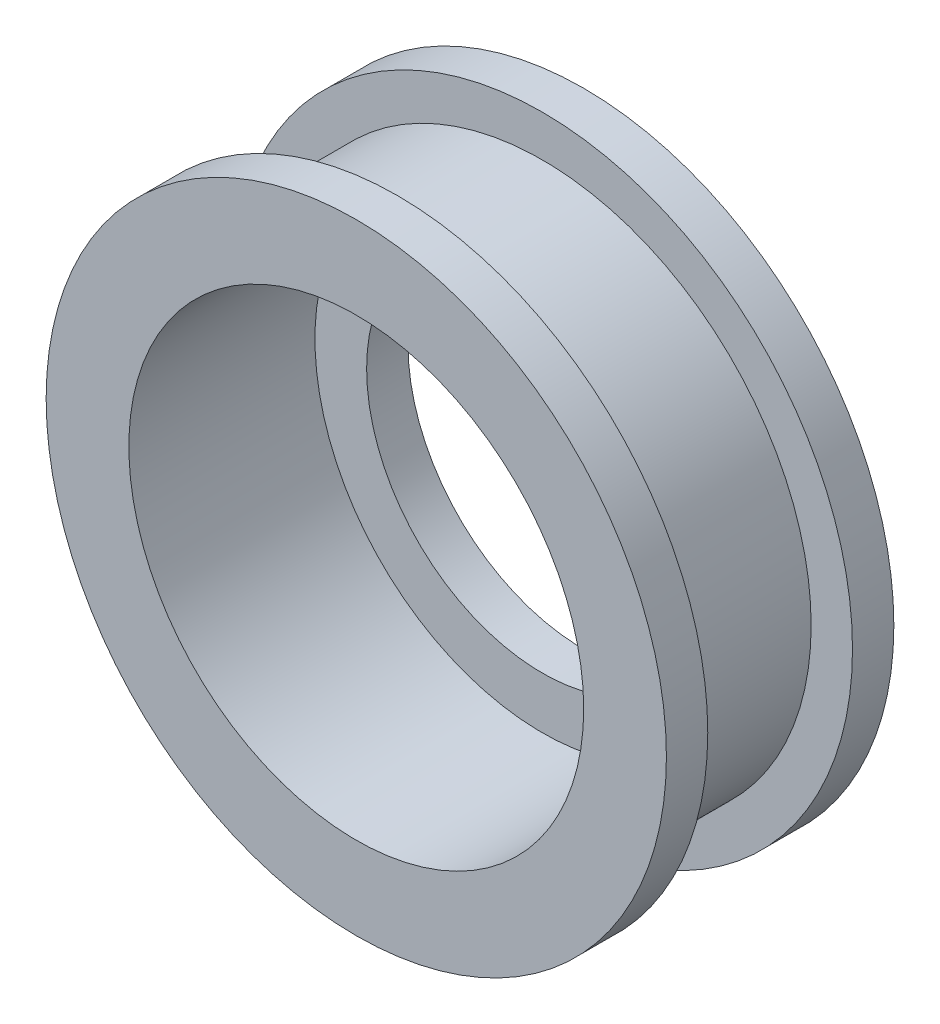
SolidWorks part; units mm, degrees
ref_plane "Alzado" through (0, 0, 0) normal (0, 0, 1) x (1, 0, 0)
ref_plane "Planta" through (0, 0, 0) normal (0, 1, 0) x (1, 0, 0)
ref_plane "Vista lateral" through (0, 0, 0) normal (1, 0, 0) x (0, 0, -1)
sketch "Croquis1" plane through (0, 0, 0) normal (0, 0, 1) x (1, 0, 0)
  circle A0 centre (0, 0) radius 15
  circle A1 centre (0, 0) radius 8.5
  dimension "D1" = 17
  dimension "D2" = 30
extrude "Saliente-Extruir1" add sketch "Croquis1" along normal blind 2
sketch "Croquis2" plane through (0, 0, 2) normal (0, 0, 1) x (1, 0, 0)
  circle A0 centre (0, 0) radius 11
  circle A1 centre (0, 0) radius 13
  dimension "D1" = 26
  dimension "D2" = 22
extrude "Saliente-Extruir2" add sketch "Croquis2" along normal blind 7
sketch "Croquis3" plane through (0, 0, 9) normal (0, 0, 1) x (1, 0, 0)
  circle A0 centre (0, 0) radius 11
  circle A1 centre (0, 0) radius 15
  dimension "D1" = 30
extrude "Saliente-Extruir3" add sketch "Croquis3" along normal blind 2
